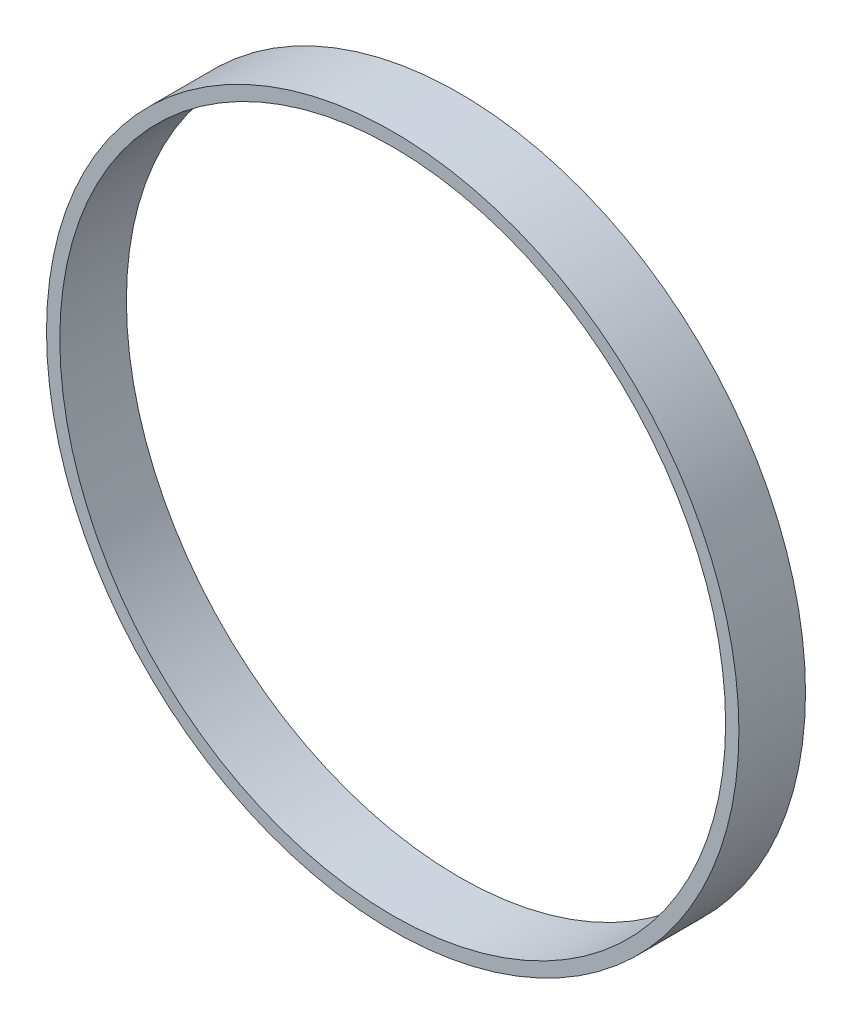
SolidWorks part; units mm, degrees
ref_plane "Front Plane" through (0, 0, 0) normal (0, 0, 1) x (1, 0, 0)
ref_plane "Top Plane" through (0, 0, 0) normal (0, 1, 0) x (1, 0, 0)
ref_plane "Right Plane" through (0, 0, 0) normal (1, 0, 0) x (0, 0, -1)
sketch "Sketch1" plane through (0, 0, 0) normal (0, 0, 1) x (1, 0, 0)
  line L0 (42.5461, 90.4977) -> (44.248, 94.1176) construction
  circle A0 centre (0, 0) radius 100
  circle A1 centre (0, 0) radius 104
  dimension "D2" = 200
  dimension "D1" = 4
extrude "Boss-Extrude1" add sketch "Sketch1" along normal blind 20
sketch3d "URDF Reference"
  line L0 (0, 0, 0) -> (10, 0, 0) construction
  line L1 (0, 0, 0) -> (0, 0, -10) construction
  point P0 (0, 0, 0)
  point P1 (0, 0, 0)
